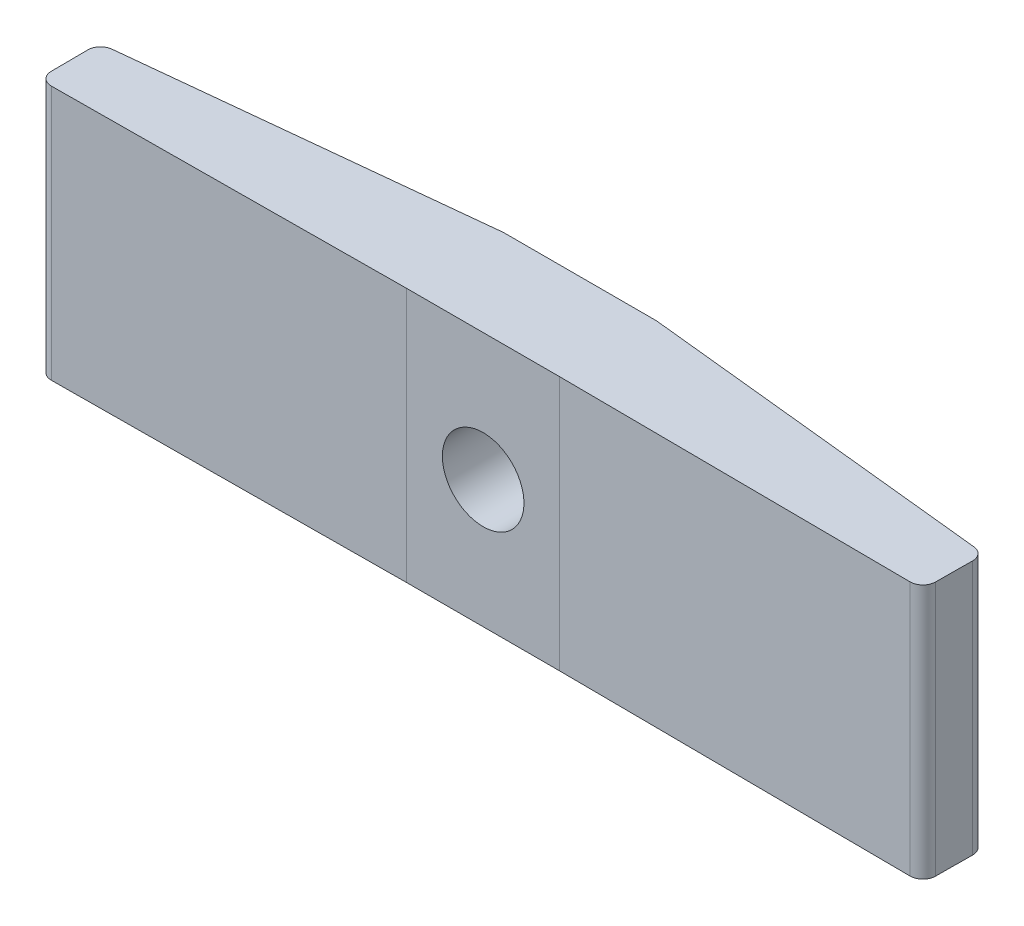
SolidWorks part; units mm, degrees
ref_plane "Front" through (0, 0, 0) normal (0, 0, 1) x (1, 0, 0)
ref_plane "Top" through (0, 0, 0) normal (0, 1, 0) x (1, 0, 0)
ref_plane "Right" through (0, 0, 0) normal (1, 0, 0) x (0, 0, -1)
sketch "Sketch1" plane through (0, 0, 0) normal (0, 1, 0) x (1, 0, 0)
  line L0 (0, 0) -> (34.7, 0) construction
  line L1 (17.35, 0) -> (17.35, 17.8266) construction
  line L2 (20.35, 0.1) -> (14.35, 0.1)
  line L3 (14.35, 0.1) -> (0, 0)
  line L4 (0, 0) -> (-0.0167, 2.4)
  line L9 (20.35, 3.9) -> (34.7167, 2.4)
  line L10 (20.35, 3.9) -> (14.35, 3.9)
  line L11 (14.35, 3.9) -> (-0.0167, 2.4)
  line L14 (34.7, 0) -> (34.7167, 2.4)
  line L15 (20.35, 0.1) -> (34.7, 0)
  line L16 (14.35, 3.9) -> (14.35, 0.1) construction
  point P25 (17.35, 3.9)
  point P26 (17.35, 2.4)
  point P28 (17.35, 2.2)
  point P29 (17.35, 0.1)
  dimension "D1" = 34.7
  dimension "D2" = 0.2
  dimension "D3" = 3.8
  dimension "D4" = 1.5
  dimension "D6" = 6
  dimension "D8" = 2.4
extrude "Boss-Extrude1" add sketch "Sketch1" along normal blind 10
fillet "Fillet1" [suppressed] radius 0.1
fillet "Fillet2" radius 0.5 4 edges at (-0.0167, 5, -2.4) (34.7167, 5, -2.4) (34.7, 5, 0) (0, 5, 0)
sketch "Sketch2" plane through (0, 0, -3.9) normal (0, 0, -1) x (-1, 0, 0)
  line L0 (-17.35, 5) -> (-17.35, 0) construction
  line L1 (-20.35, 0) -> (-14.35, 0) construction
  line L2 (-17.35, 5) -> (-17.35, 10) construction
  line L3 (-20.35, 10) -> (-14.35, 10) construction
  circle A0 centre (-17.35, 5) radius 1.6
  dimension "D1" = 3.2
extrude "Cut-Extrude1" cut sketch "Sketch2" against normal through all
sketch "Sketch3" plane through (0.6222, 0, -5.9597) normal (0.1038, 0, -0.9946) x (-0.9946, 0, -0.1038)
  line L0 (-33.8261, 1) -> (-19.835, 1) construction
  line L1 (-33.8261, 10) -> (-33.8261, 0) construction
  line L2 (-19.835, 10) -> (-19.835, 0) construction
  line L4 (-33.8261, 0) -> (-19.835, 0) construction
  text T0 "BCL" font "Century Gothic" height in points 20
  dimension "D1" = 1
extrude "Boss-Extrude2" [suppressed] add sketch "Sketch3" along normal blind 0.4
sketch "Sketch4" plane through (-0.2481, 0, -2.3758) normal (-0.1038, 0, -0.9946) x (-0.9946, 0, 0.1038)
  line L0 (-14.6774, 1) -> (-0.6863, 1) construction
  line L1 (-14.6774, 10) -> (-14.6774, 0) construction
  line L2 (-0.6863, 0) -> (-0.6863, 10) construction
  line L3 (-14.6774, 0) -> (-0.6863, 0) construction
  text T0 "02" font "Century Gothic" height in points 20
  dimension "D1" = 1
extrude "Boss-Extrude3" [suppressed] add sketch "Sketch4" along normal blind 0.4
sketch "Sketch5" plane through (-0.2481, 0, -2.3758) normal (-0.1038, 0, -0.9946) x (-0.9946, 0, 0.1038)
  line L0 (-14.6774, 1) -> (-0.6863, 1) construction
  line L1 (-14.6774, 10) -> (-14.6774, 0) construction
  line L2 (-0.6863, 0) -> (-0.6863, 10) construction
  line L3 (-14.6774, 0) -> (-0.6863, 0) construction
  text T0 "...."
  dimension "D1" = 1
extrude "revision indication" add sketch "Sketch5" along normal blind 0.4
